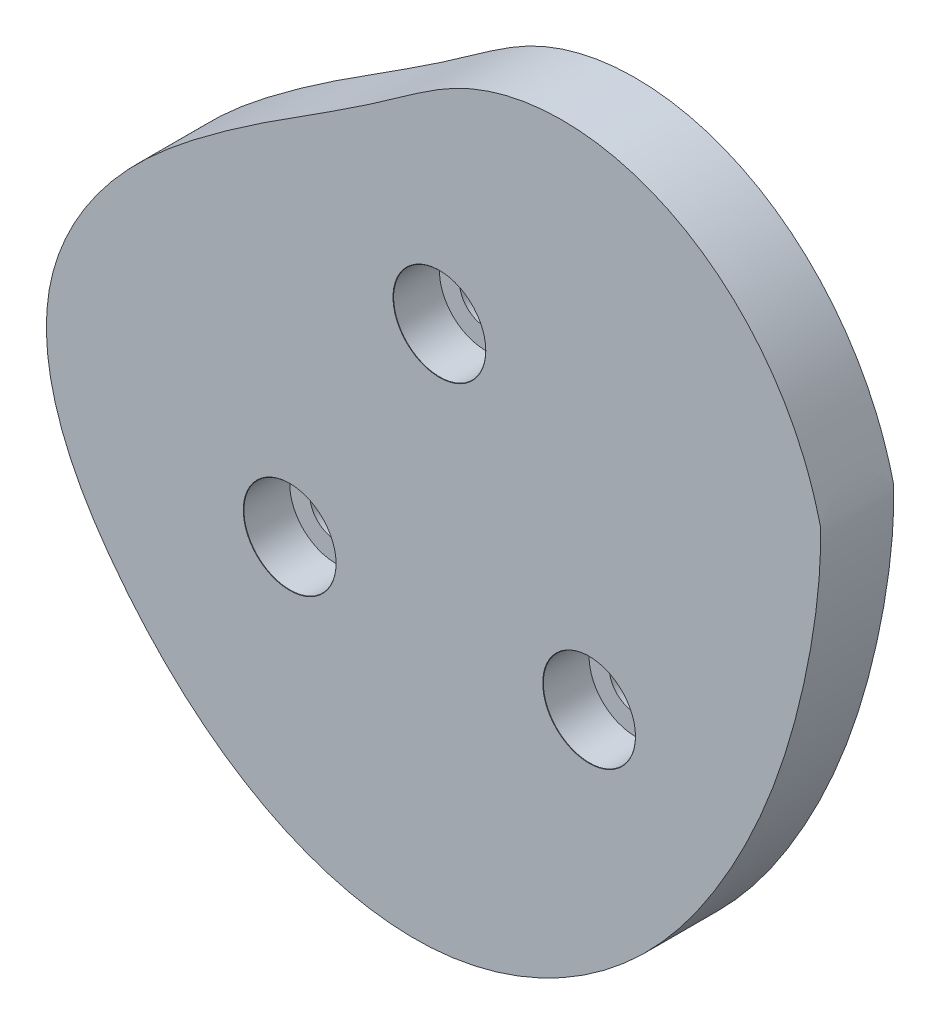
SolidWorks part; units mm, degrees
ref_plane "Front Plane" through (0, 0, 0) normal (0, 0, 1) x (1, 0, 0)
ref_plane "Top Plane" through (0, 0, 0) normal (0, 1, 0) x (1, 0, 0)
ref_plane "Right Plane" through (0, 0, 0) normal (1, 0, 0) x (0, 0, -1)
curve "Curve1"
  spline degree 3 poles (20.4719, -0.3582, 0) (20.4906, 0.0056, 0) (20.3791, 0.3547, 0) (20.2968, 0.7085, 0) (20.2014, 1.0583, 0) (20.1045, 1.4055, 0) (20.003, 1.7496, 0) (19.8979, 2.091, 0) (19.7889, 2.4294, 0) (19.6761, 2.7649, 0) (19.5596, 3.0976, 0) (19.4394, 3.4274, 0) (19.3156, 3.7542, 0) (19.1882, 4.0783, 0) (19.0573, 4.3994, 0) (18.9228, 4.7177, 0) (18.7848, 5.0331, 0) (18.6433, 5.3456, 0) (18.4984, 5.6553, 0) (18.3501, 5.962, 0) (18.1985, 6.266, 0) (18.0434, 6.567, 0) (17.8851, 6.8652, 0) (17.7235, 7.1605, 0) (17.5586, 7.4529, 0) (17.3904, 7.7425, 0) (17.219, 8.0291, 0) (17.0444, 8.3129, 0) (16.8666, 8.5937, 0) (16.6856, 8.8717, 0) (16.5014, 9.1467, 0) (16.3141, 9.4188, 0) (16.1237, 9.6879, 0) (15.9302, 9.9541, 0) (15.7336, 10.2173, 0) (15.5338, 10.4776, 0) (15.3311, 10.7348, 0) (15.1252, 10.989, 0) (14.9164, 11.2402, 0) (14.7045, 11.4883, 0) (14.4895, 11.7333, 0) (14.2716, 11.9752, 0) (14.0507, 12.214, 0) (13.8268, 12.4496, 0) (13.5999, 12.6821, 0) (13.3701, 12.9113, 0) (13.1374, 13.1373, 0) (12.9017, 13.3601, 0) (12.6631, 13.5795, 0) (12.4217, 13.7956, 0) (12.1773, 14.0084, 0) (11.9301, 14.2177, 0) (11.68, 14.4236, 0) (11.4271, 14.626, 0) (11.1713, 14.8249, 0) (10.9128, 15.0202, 0) (10.6515, 15.212, 0) (10.3875, 15.4001, 0) (10.1207, 15.5845, 0) (9.8512, 15.7652, 0) (9.579, 15.9422, 0) (9.3041, 16.1153, 0) (9.0266, 16.2845, 0) (8.7465, 16.4499, 0) (8.4638, 16.6112, 0) (8.1785, 16.7686, 0) (7.8907, 16.9219, 0) (7.6005, 17.0711, 0) (7.3077, 17.2161, 0) (7.0126, 17.357, 0) (6.715, 17.4935, 0) (6.4152, 17.6257, 0) (6.113, 17.7536, 0) (5.8085, 17.877, 0) (5.5018, 17.996, 0) (5.193, 18.1104, 0) (4.882, 18.2202, 0) (4.5689, 18.3254, 0) (4.2539, 18.4259, 0) (3.9368, 18.5217, 0) (3.6178, 18.6126, 0) (3.297, 18.6987, 0) (2.9743, 18.7798, 0) (2.6499, 18.856, 0) (2.3239, 18.9272, 0) (1.9962, 18.9933, 0) (1.6669, 19.0543, 0) (1.3362, 19.11, 0) (1.0041, 19.1606, 0) (0.6706, 19.2059, 0) (0.3358, 19.2458, 0) (-0.0001, 19.2804, 0) (-0.3372, 19.3095, 0) (-0.6752, 19.3332, 0) (-1.0143, 19.3513, 0) (-1.3542, 19.3639, 0) (-1.6948, 19.3709, 0) (-2.0362, 19.3722, 0) (-2.3782, 19.3678, 0) (-2.7207, 19.3577, 0) (-3.0636, 19.3418, 0) (-3.4068, 19.3201, 0) (-3.7502, 19.2926, 0) (-4.0938, 19.2592, 0) (-4.4374, 19.2198, 0) (-4.7809, 19.1746, 0) (-5.1242, 19.1233, 0) (-5.4672, 19.0661, 0) (-5.8099, 19.0029, 0) (-6.152, 18.9336, 0) (-6.4935, 18.8583, 0) (-6.8343, 18.7768, 0) (-7.1743, 18.6893, 0) (-7.5133, 18.5957, 0) (-7.8512, 18.496, 0) (-8.1879, 18.3901, 0) (-8.5233, 18.2781, 0) (-8.8573, 18.16, 0) (-9.1898, 18.0358, 0) (-9.5206, 17.9054, 0) (-9.8496, 17.7689, 0) (-10.1766, 17.6262, 0) (-10.5017, 17.4775, 0) (-10.8245, 17.3227, 0) (-11.1451, 17.1617, 0) (-11.4632, 16.9947, 0) (-11.7791, 16.822, 0) (-12.0927, 16.6439, 0) (-12.4044, 16.4609, 0) (-12.7144, 16.2733, 0) (-13.0229, 16.0815, 0) (-13.3301, 15.8857, 0) (-13.6364, 15.6864, 0) (-13.9422, 15.4837, 0) (-14.2476, 15.278, 0) (-14.5531, 15.0694, 0) (-14.859, 14.8581, 0) (-15.1658, 14.6444, 0) (-15.4738, 14.4285, 0) (-15.7835, 14.2103, 0) (-16.0953, 13.99, 0) (-16.4096, 13.7678, 0) (-16.7269, 13.5435, 0) (-17.0477, 13.3173, 0) (-17.3725, 13.0891, 0) (-17.7016, 12.8589, 0) (-18.0357, 12.6265, 0) (-18.3753, 12.3918, 0) (-18.7207, 12.1548, 0) (-19.0726, 11.9151, 0) (-19.4314, 11.6726, 0) (-19.7976, 11.4271, 0) (-20.1718, 11.1782, 0) (-20.5544, 10.9256, 0) (-20.9459, 10.669, 0) (-21.3468, 10.4079, 0) (-21.7576, 10.142, 0) (-22.1787, 9.8708, 0) (-22.6107, 9.5937, 0) (-23.0538, 9.3103, 0) (-23.5087, 9.0201, 0) (-23.9757, 8.7223, 0) (-24.4552, 8.4163, 0) (-24.9476, 8.1016, 0) (-25.4532, 7.7775, 0) (-25.9724, 7.443, 0) (-26.5055, 7.0977, 0) (-27.0528, 6.7405, 0) (-27.6146, 6.3708, 0) (-28.1911, 5.9877, 0) (-28.7826, 5.5902, 0) (-29.3891, 5.1775, 0) (-30.011, 4.7487, 0) (-30.6482, 4.3027, 0) (-31.3009, 3.8387, 0) (-31.9692, 3.3555, 0) (-32.6531, 2.8522, 0) (-33.3524, 2.3277, 0) (-34.0663, 1.7816, 0) (-34.7922, 1.212, 0) (-35.5264, 0.6179, 0) (-36.2656, -0.0015, 0) (-37.006, -0.6467, 0) (-37.7441, -1.3181, 0) (-38.4762, -2.0158, 0) (-39.1988, -2.7397, 0) (-39.9081, -3.4895, 0) (-40.6005, -4.2646, 0) (-41.2726, -5.0643, 0) (-41.9207, -5.8876, 0) (-42.5414, -6.7333, 0) (-43.1312, -7.6, 0) (-43.6867, -8.4861, 0) (-44.2047, -9.3896, 0) (-44.6819, -10.3087, 0) (-45.1152, -11.2411, 0) (-45.5015, -12.1842, 0) (-45.838, -13.1356, 0) (-46.1218, -14.0922, 0) (-46.3502, -15.0514, 0) (-46.5207, -16.0105, 0) (-46.6353, -16.9668, 0) (-46.6959, -17.9187, 0) (-46.7048, -18.8646, 0) (-46.6641, -19.8031, 0) (-46.576, -20.7331, 0) (-46.4429, -21.6534, 0) (-46.2667, -22.5631, 0) (-46.0499, -23.4614, 0) (-45.7945, -24.3476, 0) (-45.5028, -25.2212, 0) (-45.1769, -26.0818, 0) (-44.8189, -26.9291, 0) (-44.431, -27.763, 0) (-44.0152, -28.5834, 0) (-43.5736, -29.3905, 0) (-43.1082, -30.1845, 0) (-42.6208, -30.9657, 0) (-42.1134, -31.7347, 0) (-41.5877, -32.4919, 0) (-41.0455, -33.2381, 0) (-40.4886, -33.9741, 0) (-39.9184, -34.7007, 0) (-39.3348, -35.4173, 0) (-38.7375, -36.1234, 0) (-38.1264, -36.8183, 0) (-37.5012, -37.5012, 0) (-36.8618, -38.1715, 0) (-36.2081, -38.8285, 0) (-35.5401, -39.4713, 0) (-34.8578, -40.0993, 0) (-34.1611, -40.7116, 0) (-33.4502, -41.3075, 0) (-32.725, -41.8861, 0) (-31.9858, -42.4467, 0) (-31.2328, -42.9883, 0) (-30.4661, -43.5102, 0) (-29.686, -44.0114, 0) (-28.8928, -44.4912, 0) (-28.0869, -44.9487, 0) (-27.2687, -45.383, 0) (-26.4385, -45.7933, 0) (-25.5969, -46.1786, 0) (-24.7444, -46.5382, 0) (-23.8816, -46.8712, 0) (-23.009, -47.1767, 0) (-22.1274, -47.454, 0) (-21.2375, -47.7021, 0) (-20.34, -47.9203, 0) (-19.4357, -48.1077, 0) (-18.5254, -48.2636, 0) (-17.6101, -48.3873, 0) (-16.6907, -48.4779, 0) (-15.7681, -48.5348, 0) (-14.8434, -48.5572, 0) (-13.9176, -48.5444, 0) (-12.9919, -48.4959, 0) (-12.0676, -48.4109, 0) (-11.1461, -48.29, 0) (-10.2287, -48.1341, 0) (-9.3169, -47.9441, 0) (-8.412, -47.7209, 0) (-7.5154, -47.4656, 0) (-6.6283, -47.1791, 0) (-5.7518, -46.8626, 0) (-4.887, -46.5172, 0) (-4.035, -46.144, 0) (-3.1968, -45.7443, 0) (-2.3733, -45.3192, 0) (-1.5652, -44.87, 0) (-0.7734, -44.398, 0) (0.0014, -43.9045, 0) (0.7587, -43.3908, 0) (1.4978, -42.8582, 0) (2.2183, -42.3081, 0) (2.9197, -41.7419, 0) (3.6018, -41.1608, 0) (4.2642, -40.5664, 0) (4.9068, -39.9599, 0) (5.5294, -39.3427, 0) (6.132, -38.7162, 0) (6.7146, -38.0817, 0) (7.2773, -37.4407, 0) (7.8203, -36.7944, 0) (8.3437, -36.1442, 0) (8.8479, -35.4914, 0) (9.3333, -34.8372, 0) (9.8003, -34.183, 0) (10.2494, -33.5299, 0) (10.6811, -32.8793, 0) (11.0962, -32.2321, 0) (11.4952, -31.5897, 0) (11.8791, -30.953, 0) (12.2485, -30.3226, 0) (12.6037, -29.6986, 0) (12.9452, -29.0811, 0) (13.2733, -28.4704, 0) (13.5887, -27.8663, 0) (13.8917, -27.2691, 0) (14.1827, -26.6788, 0) (14.4623, -26.0953, 0) (14.7307, -25.5188, 0) (14.9884, -24.9492, 0) (15.2358, -24.3866, 0) (15.4733, -23.8309, 0) (15.7014, -23.2821, 0) (15.9202, -22.7402, 0) (16.1303, -22.2051, 0) (16.332, -21.6768, 0) (16.5257, -21.1552, 0) (16.7115, -20.6403, 0) (16.89, -20.1319, 0) (17.0614, -19.63, 0) (17.2261, -19.1344, 0) (17.3842, -18.6451, 0) (17.5361, -18.1619, 0) (17.6822, -17.6848, 0) (17.8225, -17.2135, 0) (17.9574, -16.748, 0) (18.0872, -16.2881, 0) (18.2121, -15.8337, 0) (18.3322, -15.3847, 0) (18.4478, -14.9408, 0) (18.5591, -14.5019, 0) (18.6662, -14.0679, 0) (18.7694, -13.6386, 0) (18.8688, -13.2138, 0) (18.9646, -12.7934, 0) (19.0568, -12.3772, 0) (19.1457, -11.9651, 0) (19.2313, -11.5568, 0) (19.3138, -11.1522, 0) (19.3933, -10.7511, 0) (19.4697, -10.3534, 0) (19.5433, -9.959, 0) (19.6141, -9.5675, 0) (19.6821, -9.1789, 0) (19.7474, -8.7931, 0) (19.8101, -8.4098, 0) (19.87, -8.0288, 0) (19.9274, -7.6502, 0) (19.9821, -7.2736, 0) (20.0342, -6.899, 0) (20.0836, -6.5262, 0) (20.1304, -6.1551, 0) (20.1746, -5.7855, 0) (20.216, -5.4173, 0) (20.2547, -5.0505, 0) (20.2905, -4.6848, 0) (20.3236, -4.3203, 0) (20.3537, -3.9567, 0) (20.3809, -3.594, 0) (20.4049, -3.2321, 0) (20.4259, -2.8709, 0) (20.4437, -2.5104, 0) (20.4581, -2.1504, 0) (20.4692, -1.791, 0) (20.4769, -1.432, 0) (20.4803, -1.0735, 0) (20.4824, -0.7151, 0) (20.4719, -0.3582, 0) (20.4906, 0.0056, 0) (20.3791, 0.3547, 0) knots -0.005175 -0.003449 -0.001724 0 0.001764 0.003519 0.005266 0.007004 0.008734 0.010456 0.01217 0.013877 0.015576 0.017268 0.018953 0.020632 0.022304 0.02397 0.02563 0.027283 0.028932 0.030575 0.032212 0.033845 0.035472 0.037095 0.038714 0.040328 0.041938 0.043545 0.045147 0.046746 0.048342 0.049935 0.051524 0.053111 0.054695 0.056276 0.057855 0.059432 0.061007 0.06258 0.064152 0.065721 0.06729 0.068857 0.070423 0.071988 0.073552 0.075115 0.076678 0.07824 0.079802 0.081364 0.082926 0.084488 0.08605 0.087612 0.089174 0.090737 0.092301 0.093865 0.095431 0.096997 0.098564 0.100132 0.101701 0.103272 0.104844 0.106418 0.107993 0.109569 0.111148 0.112728 0.11431 0.115894 0.117479 0.119067 0.120657 0.12225 0.123844 0.125441 0.12704 0.128642 0.130246 0.131852 0.133461 0.135073 0.136687 0.138304 0.139924 0.141547 0.143172 0.1448 0.146431 0.148065 0.149702 0.151342 0.152985 0.154631 0.156279 0.157931 0.159586 0.161244 0.162905 0.16457 0.166237 0.167907 0.169581 0.171258 0.172937 0.17462 0.176307 0.177996 0.179688 0.181384 0.183082 0.184784 0.186489 0.188197 0.189908 0.191622 0.19334 0.19506 0.196783 0.19851 0.200239 0.201971 0.203707 0.205446 0.207188 0.208935 0.210686 0.212442 0.214204 0.215972 0.217748 0.219531 0.221323 0.223125 0.224939 0.226765 0.228604 0.23046 0.232333 0.234225 0.236138 0.238074 0.240035 0.242024 0.244043 0.246095 0.248182 0.250307 0.252473 0.254682 0.256938 0.259244 0.261602 0.264016 0.26649 0.269025 0.271625 0.274295 0.277036 0.279852 0.282747 0.285724 0.288785 0.291935 0.295176 0.298513 0.301947 0.305484 0.309124 0.312873 0.316734 0.320709 0.324801 0.329015 0.333352 0.337803 0.34236 0.347013 0.351751 0.356565 0.361444 0.366378 0.371357 0.376371 0.38141 0.386464 0.391524 0.39658 0.401624 0.406647 0.411641 0.416599 0.421513 0.426378 0.431188 0.43594 0.440632 0.445271 0.449865 0.454421 0.458946 0.463447 0.467927 0.472391 0.476844 0.481289 0.485727 0.490163 0.494596 0.499029 0.503463 0.507898 0.512334 0.516773 0.521215 0.525659 0.530106 0.534555 0.539008 0.543464 0.547923 0.552384 0.556848 0.561315 0.565783 0.570252 0.574723 0.579195 0.583667 0.588139 0.592612 0.597084 0.601555 0.606025 0.610494 0.614962 0.619428 0.623892 0.628354 0.632814 0.637273 0.641729 0.646184 0.650638 0.65509 0.659542 0.663994 0.668446 0.672899 0.677354 0.681812 0.686275 0.690742 0.695217 0.699697 0.704183 0.708673 0.713166 0.717661 0.722155 0.726648 0.731137 0.735622 0.740099 0.744568 0.749025 0.75347 0.757899 0.762311 0.766703 0.771074 0.775421 0.779741 0.784033 0.788293 0.792521 0.796712 0.800866 0.804979 0.809049 0.813074 0.817052 0.82098 0.824856 0.828677 0.832443 0.83615 0.839797 0.843382 0.846904 0.850365 0.853767 0.857109 0.860394 0.863623 0.866796 0.869914 0.87298 0.875994 0.878957 0.88187 0.884735 0.887552 0.890324 0.89305 0.895732 0.898371 0.900968 0.903525 0.906043 0.908522 0.910963 0.913369 0.915739 0.918076 0.920379 0.922651 0.924892 0.927103 0.929285 0.93144 0.933569 0.935672 0.93775 0.939805 0.941838 0.943849 0.94584 0.94781 0.949763 0.951697 0.953615 0.955517 0.957403 0.959276 0.961134 0.962981 0.964815 0.966638 0.968451 0.970255 0.972049 0.973835 0.975613 0.977385 0.979149 0.980908 0.982662 0.98441 0.986154 0.987894 0.989631 0.991365 0.993096 0.994825 0.996551 0.998276 1 1.001764 1.003519 1.005266 periodic
sketch "Sketch1" plane through (0, 0, 0) normal (0, 0, 1) x (1, 0, 0)
  spline S0 degree 3 poles (20.4719, -0.3582) (20.4906, 0.0056) (20.3791, 0.3547) (20.2968, 0.7085) (20.2014, 1.0583) (20.1045, 1.4055) (20.003, 1.7496) (19.8979, 2.091) (19.7889, 2.4294) (19.6761, 2.7649) (19.5596, 3.0976) (19.4394, 3.4274) (19.3156, 3.7542) (19.1882, 4.0783) (19.0573, 4.3994) (18.9228, 4.7177) (18.7848, 5.0331) (18.6433, 5.3456) (18.4984, 5.6553) (18.3501, 5.962) (18.1985, 6.266) (18.0434, 6.567) (17.8851, 6.8652) (17.7235, 7.1605) (17.5586, 7.4529) (17.3904, 7.7425) (17.219, 8.0291) (17.0444, 8.3129) (16.8666, 8.5937) (16.6856, 8.8717) (16.5014, 9.1467) (16.3141, 9.4188) (16.1237, 9.6879) (15.9302, 9.9541) (15.7336, 10.2173) (15.5338, 10.4776) (15.3311, 10.7348) (15.1252, 10.989) (14.9164, 11.2402) (14.7045, 11.4883) (14.4895, 11.7333) (14.2716, 11.9752) (14.0507, 12.214) (13.8268, 12.4496) (13.5999, 12.6821) (13.3701, 12.9113) (13.1374, 13.1373) (12.9017, 13.3601) (12.6631, 13.5795) (12.4217, 13.7956) (12.1773, 14.0084) (11.9301, 14.2177) (11.68, 14.4236) (11.4271, 14.626) (11.1713, 14.8249) (10.9128, 15.0202) (10.6515, 15.212) (10.3875, 15.4001) (10.1207, 15.5845) (9.8512, 15.7652) (9.579, 15.9422) (9.3041, 16.1153) (9.0266, 16.2845) (8.7465, 16.4499) (8.4638, 16.6112) (8.1785, 16.7686) (7.8907, 16.9219) (7.6005, 17.0711) (7.3077, 17.2161) (7.0126, 17.357) (6.715, 17.4935) (6.4152, 17.6257) (6.113, 17.7536) (5.8085, 17.877) (5.5018, 17.996) (5.193, 18.1104) (4.882, 18.2202) (4.5689, 18.3254) (4.2539, 18.4259) (3.9368, 18.5217) (3.6178, 18.6126) (3.297, 18.6987) (2.9743, 18.7798) (2.6499, 18.856) (2.3239, 18.9272) (1.9962, 18.9933) (1.6669, 19.0543) (1.3362, 19.11) (1.0041, 19.1606) (0.6706, 19.2059) (0.3358, 19.2458) (-0.0001, 19.2804) (-0.3372, 19.3095) (-0.6752, 19.3332) (-1.0143, 19.3513) (-1.3542, 19.3639) (-1.6948, 19.3709) (-2.0362, 19.3722) (-2.3782, 19.3678) (-2.7207, 19.3577) (-3.0636, 19.3418) (-3.4068, 19.3201) (-3.7502, 19.2926) (-4.0938, 19.2592) (-4.4374, 19.2198) (-4.7809, 19.1746) (-5.1242, 19.1233) (-5.4672, 19.0661) (-5.8099, 19.0029) (-6.152, 18.9336) (-6.4935, 18.8583) (-6.8343, 18.7768) (-7.1743, 18.6893) (-7.5133, 18.5957) (-7.8512, 18.496) (-8.1879, 18.3901) (-8.5233, 18.2781) (-8.8573, 18.16) (-9.1898, 18.0358) (-9.5206, 17.9054) (-9.8496, 17.7689) (-10.1766, 17.6262) (-10.5017, 17.4775) (-10.8245, 17.3227) (-11.1451, 17.1617) (-11.4632, 16.9947) (-11.7791, 16.822) (-12.0927, 16.6439) (-12.4044, 16.4609) (-12.7144, 16.2733) (-13.0229, 16.0815) (-13.3301, 15.8857) (-13.6364, 15.6864) (-13.9422, 15.4837) (-14.2476, 15.278) (-14.5531, 15.0694) (-14.859, 14.8581) (-15.1658, 14.6444) (-15.4738, 14.4285) (-15.7835, 14.2103) (-16.0953, 13.99) (-16.4096, 13.7678) (-16.7269, 13.5435) (-17.0477, 13.3173) (-17.3725, 13.0891) (-17.7016, 12.8589) (-18.0357, 12.6265) (-18.3753, 12.3918) (-18.7207, 12.1548) (-19.0726, 11.9151) (-19.4314, 11.6726) (-19.7976, 11.4271) (-20.1718, 11.1782) (-20.5544, 10.9256) (-20.9459, 10.669) (-21.3468, 10.4079) (-21.7576, 10.142) (-22.1787, 9.8708) (-22.6107, 9.5937) (-23.0538, 9.3103) (-23.5087, 9.0201) (-23.9757, 8.7223) (-24.4552, 8.4163) (-24.9476, 8.1016) (-25.4532, 7.7775) (-25.9724, 7.443) (-26.5055, 7.0977) (-27.0528, 6.7405) (-27.6146, 6.3708) (-28.1911, 5.9877) (-28.7826, 5.5902) (-29.3891, 5.1775) (-30.011, 4.7487) (-30.6482, 4.3027) (-31.3009, 3.8387) (-31.9692, 3.3555) (-32.6531, 2.8522) (-33.3524, 2.3277) (-34.0663, 1.7816) (-34.7922, 1.212) (-35.5264, 0.6179) (-36.2656, -0.0015) (-37.006, -0.6467) (-37.7441, -1.3181) (-38.4762, -2.0158) (-39.1988, -2.7397) (-39.9081, -3.4895) (-40.6005, -4.2646) (-41.2726, -5.0643) (-41.9207, -5.8876) (-42.5414, -6.7333) (-43.1312, -7.6) (-43.6867, -8.4861) (-44.2047, -9.3896) (-44.6819, -10.3087) (-45.1152, -11.2411) (-45.5015, -12.1842) (-45.838, -13.1356) (-46.1218, -14.0922) (-46.3502, -15.0514) (-46.5207, -16.0105) (-46.6353, -16.9668) (-46.6959, -17.9187) (-46.7048, -18.8646) (-46.6641, -19.8031) (-46.576, -20.7331) (-46.4429, -21.6534) (-46.2667, -22.5631) (-46.0499, -23.4614) (-45.7945, -24.3476) (-45.5028, -25.2212) (-45.1769, -26.0818) (-44.8189, -26.9291) (-44.431, -27.763) (-44.0152, -28.5834) (-43.5736, -29.3905) (-43.1082, -30.1845) (-42.6208, -30.9657) (-42.1134, -31.7347) (-41.5877, -32.4919) (-41.0455, -33.2381) (-40.4886, -33.9741) (-39.9184, -34.7007) (-39.3348, -35.4173) (-38.7375, -36.1234) (-38.1264, -36.8183) (-37.5012, -37.5012) (-36.8618, -38.1715) (-36.2081, -38.8285) (-35.5401, -39.4713) (-34.8578, -40.0993) (-34.1611, -40.7116) (-33.4502, -41.3075) (-32.725, -41.8861) (-31.9858, -42.4467) (-31.2328, -42.9883) (-30.4661, -43.5102) (-29.686, -44.0114) (-28.8928, -44.4912) (-28.0869, -44.9487) (-27.2687, -45.383) (-26.4385, -45.7933) (-25.5969, -46.1786) (-24.7444, -46.5382) (-23.8816, -46.8712) (-23.009, -47.1767) (-22.1274, -47.454) (-21.2375, -47.7021) (-20.34, -47.9203) (-19.4357, -48.1077) (-18.5254, -48.2636) (-17.6101, -48.3873) (-16.6907, -48.4779) (-15.7681, -48.5348) (-14.8434, -48.5572) (-13.9176, -48.5444) (-12.9919, -48.4959) (-12.0676, -48.4109) (-11.1461, -48.29) (-10.2287, -48.1341) (-9.3169, -47.9441) (-8.412, -47.7209) (-7.5154, -47.4656) (-6.6283, -47.1791) (-5.7518, -46.8626) (-4.887, -46.5172) (-4.035, -46.144) (-3.1968, -45.7443) (-2.3733, -45.3192) (-1.5652, -44.87) (-0.7734, -44.398) (0.0014, -43.9045) (0.7587, -43.3908) (1.4978, -42.8582) (2.2183, -42.3081) (2.9197, -41.7419) (3.6018, -41.1608) (4.2642, -40.5664) (4.9068, -39.9599) (5.5294, -39.3427) (6.132, -38.7162) (6.7146, -38.0817) (7.2773, -37.4407) (7.8203, -36.7944) (8.3437, -36.1442) (8.8479, -35.4914) (9.3333, -34.8372) (9.8003, -34.183) (10.2494, -33.5299) (10.6811, -32.8793) (11.0962, -32.2321) (11.4952, -31.5897) (11.8791, -30.953) (12.2485, -30.3226) (12.6037, -29.6986) (12.9452, -29.0811) (13.2733, -28.4704) (13.5887, -27.8663) (13.8917, -27.2691) (14.1827, -26.6788) (14.4623, -26.0953) (14.7307, -25.5188) (14.9884, -24.9492) (15.2358, -24.3866) (15.4733, -23.8309) (15.7014, -23.2821) (15.9202, -22.7402) (16.1303, -22.2051) (16.332, -21.6768) (16.5257, -21.1552) (16.7115, -20.6403) (16.89, -20.1319) (17.0614, -19.63) (17.2261, -19.1344) (17.3842, -18.6451) (17.5361, -18.1619) (17.6822, -17.6848) (17.8225, -17.2135) (17.9574, -16.748) (18.0872, -16.2881) (18.2121, -15.8337) (18.3322, -15.3847) (18.4478, -14.9408) (18.5591, -14.5019) (18.6662, -14.0679) (18.7694, -13.6386) (18.8688, -13.2138) (18.9646, -12.7934) (19.0568, -12.3772) (19.1457, -11.9651) (19.2313, -11.5568) (19.3138, -11.1522) (19.3933, -10.7511) (19.4697, -10.3534) (19.5433, -9.959) (19.6141, -9.5675) (19.6821, -9.1789) (19.7474, -8.7931) (19.8101, -8.4098) (19.87, -8.0288) (19.9274, -7.6502) (19.9821, -7.2736) (20.0342, -6.899) (20.0836, -6.5262) (20.1304, -6.1551) (20.1746, -5.7855) (20.216, -5.4173) (20.2547, -5.0505) (20.2905, -4.6848) (20.3236, -4.3203) (20.3537, -3.9567) (20.3809, -3.594) (20.4049, -3.2321) (20.4259, -2.8709) (20.4437, -2.5104) (20.4581, -2.1504) (20.4692, -1.791) (20.4769, -1.432) (20.4803, -1.0735) (20.4824, -0.7151) (20.4719, -0.3582) (20.4906, 0.0056) (20.3791, 0.3547) knots -0.005175 -0.003449 -0.001724 0 0.001764 0.003519 0.005266 0.007004 0.008734 0.010456 0.01217 0.013877 0.015576 0.017268 0.018953 0.020632 0.022304 0.02397 0.02563 0.027283 0.028932 0.030575 0.032212 0.033845 0.035472 0.037095 0.038714 0.040328 0.041938 0.043545 0.045147 0.046746 0.048342 0.049935 0.051524 0.053111 0.054695 0.056276 0.057855 0.059432 0.061007 0.06258 0.064152 0.065721 0.06729 0.068857 0.070423 0.071988 0.073552 0.075115 0.076678 0.07824 0.079802 0.081364 0.082926 0.084488 0.08605 0.087612 0.089174 0.090737 0.092301 0.093865 0.095431 0.096997 0.098564 0.100132 0.101701 0.103272 0.104844 0.106418 0.107993 0.109569 0.111148 0.112728 0.11431 0.115894 0.117479 0.119067 0.120657 0.12225 0.123844 0.125441 0.12704 0.128642 0.130246 0.131852 0.133461 0.135073 0.136687 0.138304 0.139924 0.141547 0.143172 0.1448 0.146431 0.148065 0.149702 0.151342 0.152985 0.154631 0.156279 0.157931 0.159586 0.161244 0.162905 0.16457 0.166237 0.167907 0.169581 0.171258 0.172937 0.17462 0.176307 0.177996 0.179688 0.181384 0.183082 0.184784 0.186489 0.188197 0.189908 0.191622 0.19334 0.19506 0.196783 0.19851 0.200239 0.201971 0.203707 0.205446 0.207188 0.208935 0.210686 0.212442 0.214204 0.215972 0.217748 0.219531 0.221323 0.223125 0.224939 0.226765 0.228604 0.23046 0.232333 0.234225 0.236138 0.238074 0.240035 0.242024 0.244043 0.246095 0.248182 0.250307 0.252473 0.254682 0.256938 0.259244 0.261602 0.264016 0.26649 0.269025 0.271625 0.274295 0.277036 0.279852 0.282747 0.285724 0.288785 0.291935 0.295176 0.298513 0.301947 0.305484 0.309124 0.312873 0.316734 0.320709 0.324801 0.329015 0.333352 0.337803 0.34236 0.347013 0.351751 0.356565 0.361444 0.366378 0.371357 0.376371 0.38141 0.386464 0.391524 0.39658 0.401624 0.406647 0.411641 0.416599 0.421513 0.426378 0.431188 0.43594 0.440632 0.445271 0.449865 0.454421 0.458946 0.463447 0.467927 0.472391 0.476844 0.481289 0.485727 0.490163 0.494596 0.499029 0.503463 0.507898 0.512334 0.516773 0.521215 0.525659 0.530106 0.534555 0.539008 0.543464 0.547923 0.552384 0.556848 0.561315 0.565783 0.570252 0.574723 0.579195 0.583667 0.588139 0.592612 0.597084 0.601555 0.606025 0.610494 0.614962 0.619428 0.623892 0.628354 0.632814 0.637273 0.641729 0.646184 0.650638 0.65509 0.659542 0.663994 0.668446 0.672899 0.677354 0.681812 0.686275 0.690742 0.695217 0.699697 0.704183 0.708673 0.713166 0.717661 0.722155 0.726648 0.731137 0.735622 0.740099 0.744568 0.749025 0.75347 0.757899 0.762311 0.766703 0.771074 0.775421 0.779741 0.784033 0.788293 0.792521 0.796712 0.800866 0.804979 0.809049 0.813074 0.817052 0.82098 0.824856 0.828677 0.832443 0.83615 0.839797 0.843382 0.846904 0.850365 0.853767 0.857109 0.860394 0.863623 0.866796 0.869914 0.87298 0.875994 0.878957 0.88187 0.884735 0.887552 0.890324 0.89305 0.895732 0.898371 0.900968 0.903525 0.906043 0.908522 0.910963 0.913369 0.915739 0.918076 0.920379 0.922651 0.924892 0.927103 0.929285 0.93144 0.933569 0.935672 0.93775 0.939805 0.941838 0.943849 0.94584 0.94781 0.949763 0.951697 0.953615 0.955517 0.957403 0.959276 0.961134 0.962981 0.964815 0.966638 0.968451 0.970255 0.972049 0.973835 0.975613 0.977385 0.979149 0.980908 0.982662 0.98441 0.986154 0.987894 0.989631 0.991365 0.993096 0.994825 0.996551 0.998276 1 1.001764 1.003519 1.005266 only from (20.4693, 0) to (20.4693, 0) construction
  spline S1 degree 3 poles (20.4719, -0.3582) (20.4906, 0.0056) (20.3791, 0.3547) (20.2968, 0.7085) (20.2014, 1.0583) (20.1045, 1.4055) (20.003, 1.7496) (19.8979, 2.091) (19.7889, 2.4294) (19.6761, 2.7649) (19.5596, 3.0976) (19.4394, 3.4274) (19.3156, 3.7542) (19.1882, 4.0783) (19.0573, 4.3994) (18.9228, 4.7177) (18.7848, 5.0331) (18.6433, 5.3456) (18.4984, 5.6553) (18.3501, 5.962) (18.1985, 6.266) (18.0434, 6.567) (17.8851, 6.8652) (17.7235, 7.1605) (17.5586, 7.4529) (17.3904, 7.7425) (17.219, 8.0291) (17.0444, 8.3129) (16.8666, 8.5937) (16.6856, 8.8717) (16.5014, 9.1467) (16.3141, 9.4188) (16.1237, 9.6879) (15.9302, 9.9541) (15.7336, 10.2173) (15.5338, 10.4776) (15.3311, 10.7348) (15.1252, 10.989) (14.9164, 11.2402) (14.7045, 11.4883) (14.4895, 11.7333) (14.2716, 11.9752) (14.0507, 12.214) (13.8268, 12.4496) (13.5999, 12.6821) (13.3701, 12.9113) (13.1374, 13.1373) (12.9017, 13.3601) (12.6631, 13.5795) (12.4217, 13.7956) (12.1773, 14.0084) (11.9301, 14.2177) (11.68, 14.4236) (11.4271, 14.626) (11.1713, 14.8249) (10.9128, 15.0202) (10.6515, 15.212) (10.3875, 15.4001) (10.1207, 15.5845) (9.8512, 15.7652) (9.579, 15.9422) (9.3041, 16.1153) (9.0266, 16.2845) (8.7465, 16.4499) (8.4638, 16.6112) (8.1785, 16.7686) (7.8907, 16.9219) (7.6005, 17.0711) (7.3077, 17.2161) (7.0126, 17.357) (6.715, 17.4935) (6.4152, 17.6257) (6.113, 17.7536) (5.8085, 17.877) (5.5018, 17.996) (5.193, 18.1104) (4.882, 18.2202) (4.5689, 18.3254) (4.2539, 18.4259) (3.9368, 18.5217) (3.6178, 18.6126) (3.297, 18.6987) (2.9743, 18.7798) (2.6499, 18.856) (2.3239, 18.9272) (1.9962, 18.9933) (1.6669, 19.0543) (1.3362, 19.11) (1.0041, 19.1606) (0.6706, 19.2059) (0.3358, 19.2458) (-0.0001, 19.2804) (-0.3372, 19.3095) (-0.6752, 19.3332) (-1.0143, 19.3513) (-1.3542, 19.3639) (-1.6948, 19.3709) (-2.0362, 19.3722) (-2.3782, 19.3678) (-2.7207, 19.3577) (-3.0636, 19.3418) (-3.4068, 19.3201) (-3.7502, 19.2926) (-4.0938, 19.2592) (-4.4374, 19.2198) (-4.7809, 19.1746) (-5.1242, 19.1233) (-5.4672, 19.0661) (-5.8099, 19.0029) (-6.152, 18.9336) (-6.4935, 18.8583) (-6.8343, 18.7768) (-7.1743, 18.6893) (-7.5133, 18.5957) (-7.8512, 18.496) (-8.1879, 18.3901) (-8.5233, 18.2781) (-8.8573, 18.16) (-9.1898, 18.0358) (-9.5206, 17.9054) (-9.8496, 17.7689) (-10.1766, 17.6262) (-10.5017, 17.4775) (-10.8245, 17.3227) (-11.1451, 17.1617) (-11.4632, 16.9947) (-11.7791, 16.822) (-12.0927, 16.6439) (-12.4044, 16.4609) (-12.7144, 16.2733) (-13.0229, 16.0815) (-13.3301, 15.8857) (-13.6364, 15.6864) (-13.9422, 15.4837) (-14.2476, 15.278) (-14.5531, 15.0694) (-14.859, 14.8581) (-15.1658, 14.6444) (-15.4738, 14.4285) (-15.7835, 14.2103) (-16.0953, 13.99) (-16.4096, 13.7678) (-16.7269, 13.5435) (-17.0477, 13.3173) (-17.3725, 13.0891) (-17.7016, 12.8589) (-18.0357, 12.6265) (-18.3753, 12.3918) (-18.7207, 12.1548) (-19.0726, 11.9151) (-19.4314, 11.6726) (-19.7976, 11.4271) (-20.1718, 11.1782) (-20.5544, 10.9256) (-20.9459, 10.669) (-21.3468, 10.4079) (-21.7576, 10.142) (-22.1787, 9.8708) (-22.6107, 9.5937) (-23.0538, 9.3103) (-23.5087, 9.0201) (-23.9757, 8.7223) (-24.4552, 8.4163) (-24.9476, 8.1016) (-25.4532, 7.7775) (-25.9724, 7.443) (-26.5055, 7.0977) (-27.0528, 6.7405) (-27.6146, 6.3708) (-28.1911, 5.9877) (-28.7826, 5.5902) (-29.3891, 5.1775) (-30.011, 4.7487) (-30.6482, 4.3027) (-31.3009, 3.8387) (-31.9692, 3.3555) (-32.6531, 2.8522) (-33.3524, 2.3277) (-34.0663, 1.7816) (-34.7922, 1.212) (-35.5264, 0.6179) (-36.2656, -0.0015) (-37.006, -0.6467) (-37.7441, -1.3181) (-38.4762, -2.0158) (-39.1988, -2.7397) (-39.9081, -3.4895) (-40.6005, -4.2646) (-41.2726, -5.0643) (-41.9207, -5.8876) (-42.5414, -6.7333) (-43.1312, -7.6) (-43.6867, -8.4861) (-44.2047, -9.3896) (-44.6819, -10.3087) (-45.1152, -11.2411) (-45.5015, -12.1842) (-45.838, -13.1356) (-46.1218, -14.0922) (-46.3502, -15.0514) (-46.5207, -16.0105) (-46.6353, -16.9668) (-46.6959, -17.9187) (-46.7048, -18.8646) (-46.6641, -19.8031) (-46.576, -20.7331) (-46.4429, -21.6534) (-46.2667, -22.5631) (-46.0499, -23.4614) (-45.7945, -24.3476) (-45.5028, -25.2212) (-45.1769, -26.0818) (-44.8189, -26.9291) (-44.431, -27.763) (-44.0152, -28.5834) (-43.5736, -29.3905) (-43.1082, -30.1845) (-42.6208, -30.9657) (-42.1134, -31.7347) (-41.5877, -32.4919) (-41.0455, -33.2381) (-40.4886, -33.9741) (-39.9184, -34.7007) (-39.3348, -35.4173) (-38.7375, -36.1234) (-38.1264, -36.8183) (-37.5012, -37.5012) (-36.8618, -38.1715) (-36.2081, -38.8285) (-35.5401, -39.4713) (-34.8578, -40.0993) (-34.1611, -40.7116) (-33.4502, -41.3075) (-32.725, -41.8861) (-31.9858, -42.4467) (-31.2328, -42.9883) (-30.4661, -43.5102) (-29.686, -44.0114) (-28.8928, -44.4912) (-28.0869, -44.9487) (-27.2687, -45.383) (-26.4385, -45.7933) (-25.5969, -46.1786) (-24.7444, -46.5382) (-23.8816, -46.8712) (-23.009, -47.1767) (-22.1274, -47.454) (-21.2375, -47.7021) (-20.34, -47.9203) (-19.4357, -48.1077) (-18.5254, -48.2636) (-17.6101, -48.3873) (-16.6907, -48.4779) (-15.7681, -48.5348) (-14.8434, -48.5572) (-13.9176, -48.5444) (-12.9919, -48.4959) (-12.0676, -48.4109) (-11.1461, -48.29) (-10.2287, -48.1341) (-9.3169, -47.9441) (-8.412, -47.7209) (-7.5154, -47.4656) (-6.6283, -47.1791) (-5.7518, -46.8626) (-4.887, -46.5172) (-4.035, -46.144) (-3.1968, -45.7443) (-2.3733, -45.3192) (-1.5652, -44.87) (-0.7734, -44.398) (0.0014, -43.9045) (0.7587, -43.3908) (1.4978, -42.8582) (2.2183, -42.3081) (2.9197, -41.7419) (3.6018, -41.1608) (4.2642, -40.5664) (4.9068, -39.9599) (5.5294, -39.3427) (6.132, -38.7162) (6.7146, -38.0817) (7.2773, -37.4407) (7.8203, -36.7944) (8.3437, -36.1442) (8.8479, -35.4914) (9.3333, -34.8372) (9.8003, -34.183) (10.2494, -33.5299) (10.6811, -32.8793) (11.0962, -32.2321) (11.4952, -31.5897) (11.8791, -30.953) (12.2485, -30.3226) (12.6037, -29.6986) (12.9452, -29.0811) (13.2733, -28.4704) (13.5887, -27.8663) (13.8917, -27.2691) (14.1827, -26.6788) (14.4623, -26.0953) (14.7307, -25.5188) (14.9884, -24.9492) (15.2358, -24.3866) (15.4733, -23.8309) (15.7014, -23.2821) (15.9202, -22.7402) (16.1303, -22.2051) (16.332, -21.6768) (16.5257, -21.1552) (16.7115, -20.6403) (16.89, -20.1319) (17.0614, -19.63) (17.2261, -19.1344) (17.3842, -18.6451) (17.5361, -18.1619) (17.6822, -17.6848) (17.8225, -17.2135) (17.9574, -16.748) (18.0872, -16.2881) (18.2121, -15.8337) (18.3322, -15.3847) (18.4478, -14.9408) (18.5591, -14.5019) (18.6662, -14.0679) (18.7694, -13.6386) (18.8688, -13.2138) (18.9646, -12.7934) (19.0568, -12.3772) (19.1457, -11.9651) (19.2313, -11.5568) (19.3138, -11.1522) (19.3933, -10.7511) (19.4697, -10.3534) (19.5433, -9.959) (19.6141, -9.5675) (19.6821, -9.1789) (19.7474, -8.7931) (19.8101, -8.4098) (19.87, -8.0288) (19.9274, -7.6502) (19.9821, -7.2736) (20.0342, -6.899) (20.0836, -6.5262) (20.1304, -6.1551) (20.1746, -5.7855) (20.216, -5.4173) (20.2547, -5.0505) (20.2905, -4.6848) (20.3236, -4.3203) (20.3537, -3.9567) (20.3809, -3.594) (20.4049, -3.2321) (20.4259, -2.8709) (20.4437, -2.5104) (20.4581, -2.1504) (20.4692, -1.791) (20.4769, -1.432) (20.4803, -1.0735) (20.4824, -0.7151) (20.4719, -0.3582) (20.4906, 0.0056) (20.3791, 0.3547) knots -0.005175 -0.003449 -0.001724 0 0.001764 0.003519 0.005266 0.007004 0.008734 0.010456 0.01217 0.013877 0.015576 0.017268 0.018953 0.020632 0.022304 0.02397 0.02563 0.027283 0.028932 0.030575 0.032212 0.033845 0.035472 0.037095 0.038714 0.040328 0.041938 0.043545 0.045147 0.046746 0.048342 0.049935 0.051524 0.053111 0.054695 0.056276 0.057855 0.059432 0.061007 0.06258 0.064152 0.065721 0.06729 0.068857 0.070423 0.071988 0.073552 0.075115 0.076678 0.07824 0.079802 0.081364 0.082926 0.084488 0.08605 0.087612 0.089174 0.090737 0.092301 0.093865 0.095431 0.096997 0.098564 0.100132 0.101701 0.103272 0.104844 0.106418 0.107993 0.109569 0.111148 0.112728 0.11431 0.115894 0.117479 0.119067 0.120657 0.12225 0.123844 0.125441 0.12704 0.128642 0.130246 0.131852 0.133461 0.135073 0.136687 0.138304 0.139924 0.141547 0.143172 0.1448 0.146431 0.148065 0.149702 0.151342 0.152985 0.154631 0.156279 0.157931 0.159586 0.161244 0.162905 0.16457 0.166237 0.167907 0.169581 0.171258 0.172937 0.17462 0.176307 0.177996 0.179688 0.181384 0.183082 0.184784 0.186489 0.188197 0.189908 0.191622 0.19334 0.19506 0.196783 0.19851 0.200239 0.201971 0.203707 0.205446 0.207188 0.208935 0.210686 0.212442 0.214204 0.215972 0.217748 0.219531 0.221323 0.223125 0.224939 0.226765 0.228604 0.23046 0.232333 0.234225 0.236138 0.238074 0.240035 0.242024 0.244043 0.246095 0.248182 0.250307 0.252473 0.254682 0.256938 0.259244 0.261602 0.264016 0.26649 0.269025 0.271625 0.274295 0.277036 0.279852 0.282747 0.285724 0.288785 0.291935 0.295176 0.298513 0.301947 0.305484 0.309124 0.312873 0.316734 0.320709 0.324801 0.329015 0.333352 0.337803 0.34236 0.347013 0.351751 0.356565 0.361444 0.366378 0.371357 0.376371 0.38141 0.386464 0.391524 0.39658 0.401624 0.406647 0.411641 0.416599 0.421513 0.426378 0.431188 0.43594 0.440632 0.445271 0.449865 0.454421 0.458946 0.463447 0.467927 0.472391 0.476844 0.481289 0.485727 0.490163 0.494596 0.499029 0.503463 0.507898 0.512334 0.516773 0.521215 0.525659 0.530106 0.534555 0.539008 0.543464 0.547923 0.552384 0.556848 0.561315 0.565783 0.570252 0.574723 0.579195 0.583667 0.588139 0.592612 0.597084 0.601555 0.606025 0.610494 0.614962 0.619428 0.623892 0.628354 0.632814 0.637273 0.641729 0.646184 0.650638 0.65509 0.659542 0.663994 0.668446 0.672899 0.677354 0.681812 0.686275 0.690742 0.695217 0.699697 0.704183 0.708673 0.713166 0.717661 0.722155 0.726648 0.731137 0.735622 0.740099 0.744568 0.749025 0.75347 0.757899 0.762311 0.766703 0.771074 0.775421 0.779741 0.784033 0.788293 0.792521 0.796712 0.800866 0.804979 0.809049 0.813074 0.817052 0.82098 0.824856 0.828677 0.832443 0.83615 0.839797 0.843382 0.846904 0.850365 0.853767 0.857109 0.860394 0.863623 0.866796 0.869914 0.87298 0.875994 0.878957 0.88187 0.884735 0.887552 0.890324 0.89305 0.895732 0.898371 0.900968 0.903525 0.906043 0.908522 0.910963 0.913369 0.915739 0.918076 0.920379 0.922651 0.924892 0.927103 0.929285 0.93144 0.933569 0.935672 0.93775 0.939805 0.941838 0.943849 0.94584 0.94781 0.949763 0.951697 0.953615 0.955517 0.957403 0.959276 0.961134 0.962981 0.964815 0.966638 0.968451 0.970255 0.972049 0.973835 0.975613 0.977385 0.979149 0.980908 0.982662 0.98441 0.986154 0.987894 0.989631 0.991365 0.993096 0.994825 0.996551 0.998276 1 1.001764 1.003519 1.005266 only from (20.4693, 0) to (20.4693, 0)
extrude "Boss-Extrude1" add sketch "Sketch1" along normal mid plane 6.35
sketch "Sketch4" plane through (0, 0, 3.175) normal (0, 0, 1) x (1, 0, 0)
  line L0 (17.7659, -20.9602) -> (-1.4085, -53.5016) construction
  line L1 (-50.4616, -14.4148) -> (-15.5658, 21.7389) construction
  circle A0 centre (-12.5939, -16.2726) radius 28.5365 construction
  spline S0 degree 3 poles (20.4719, -0.3582) (20.4906, 0.0056) (20.3791, 0.3547) (20.2968, 0.7085) (20.2014, 1.0583) (20.1045, 1.4055) (20.003, 1.7496) (19.8979, 2.091) (19.7889, 2.4294) (19.6761, 2.7649) (19.5596, 3.0976) (19.4394, 3.4274) (19.3156, 3.7542) (19.1882, 4.0783) (19.0573, 4.3994) (18.9228, 4.7177) (18.7848, 5.0331) (18.6433, 5.3456) (18.4984, 5.6553) (18.3501, 5.962) (18.1985, 6.266) (18.0434, 6.567) (17.8851, 6.8652) (17.7235, 7.1605) (17.5586, 7.4529) (17.3904, 7.7425) (17.219, 8.0291) (17.0444, 8.3129) (16.8666, 8.5937) (16.6856, 8.8717) (16.5014, 9.1467) (16.3141, 9.4188) (16.1237, 9.6879) (15.9302, 9.9541) (15.7336, 10.2173) (15.5338, 10.4776) (15.3311, 10.7348) (15.1252, 10.989) (14.9164, 11.2402) (14.7045, 11.4883) (14.4895, 11.7333) (14.2716, 11.9752) (14.0507, 12.214) (13.8268, 12.4496) (13.5999, 12.6821) (13.3701, 12.9113) (13.1374, 13.1373) (12.9017, 13.3601) (12.6631, 13.5795) (12.4217, 13.7956) (12.1773, 14.0084) (11.9301, 14.2177) (11.68, 14.4236) (11.4271, 14.626) (11.1713, 14.8249) (10.9128, 15.0202) (10.6515, 15.212) (10.3875, 15.4001) (10.1207, 15.5845) (9.8512, 15.7652) (9.579, 15.9422) (9.3041, 16.1153) (9.0266, 16.2845) (8.7465, 16.4499) (8.4638, 16.6112) (8.1785, 16.7686) (7.8907, 16.9219) (7.6005, 17.0711) (7.3077, 17.2161) (7.0126, 17.357) (6.715, 17.4935) (6.4152, 17.6257) (6.113, 17.7536) (5.8085, 17.877) (5.5018, 17.996) (5.193, 18.1104) (4.882, 18.2202) (4.5689, 18.3254) (4.2539, 18.4259) (3.9368, 18.5217) (3.6178, 18.6126) (3.297, 18.6987) (2.9743, 18.7798) (2.6499, 18.856) (2.3239, 18.9272) (1.9962, 18.9933) (1.6669, 19.0543) (1.3362, 19.11) (1.0041, 19.1606) (0.6706, 19.2059) (0.3358, 19.2458) (-0.0001, 19.2804) (-0.3372, 19.3095) (-0.6752, 19.3332) (-1.0143, 19.3513) (-1.3542, 19.3639) (-1.6948, 19.3709) (-2.0362, 19.3722) (-2.3782, 19.3678) (-2.7207, 19.3577) (-3.0636, 19.3418) (-3.4068, 19.3201) (-3.7502, 19.2926) (-4.0938, 19.2592) (-4.4374, 19.2198) (-4.7809, 19.1746) (-5.1242, 19.1233) (-5.4672, 19.0661) (-5.8099, 19.0029) (-6.152, 18.9336) (-6.4935, 18.8583) (-6.8343, 18.7768) (-7.1743, 18.6893) (-7.5133, 18.5957) (-7.8512, 18.496) (-8.1879, 18.3901) (-8.5233, 18.2781) (-8.8573, 18.16) (-9.1898, 18.0358) (-9.5206, 17.9054) (-9.8496, 17.7689) (-10.1766, 17.6262) (-10.5017, 17.4775) (-10.8245, 17.3227) (-11.1451, 17.1617) (-11.4632, 16.9947) (-11.7791, 16.822) (-12.0927, 16.6439) (-12.4044, 16.4609) (-12.7144, 16.2733) (-13.0229, 16.0815) (-13.3301, 15.8857) (-13.6364, 15.6864) (-13.9422, 15.4837) (-14.2476, 15.278) (-14.5531, 15.0694) (-14.859, 14.8581) (-15.1658, 14.6444) (-15.4738, 14.4285) (-15.7835, 14.2103) (-16.0953, 13.99) (-16.4096, 13.7678) (-16.7269, 13.5435) (-17.0477, 13.3173) (-17.3725, 13.0891) (-17.7016, 12.8589) (-18.0357, 12.6265) (-18.3753, 12.3918) (-18.7207, 12.1548) (-19.0726, 11.9151) (-19.4314, 11.6726) (-19.7976, 11.4271) (-20.1718, 11.1782) (-20.5544, 10.9256) (-20.9459, 10.669) (-21.3468, 10.4079) (-21.7576, 10.142) (-22.1787, 9.8708) (-22.6107, 9.5937) (-23.0538, 9.3103) (-23.5087, 9.0201) (-23.9757, 8.7223) (-24.4552, 8.4163) (-24.9476, 8.1016) (-25.4532, 7.7775) (-25.9724, 7.443) (-26.5055, 7.0977) (-27.0528, 6.7405) (-27.6146, 6.3708) (-28.1911, 5.9877) (-28.7826, 5.5902) (-29.3891, 5.1775) (-30.011, 4.7487) (-30.6482, 4.3027) (-31.3009, 3.8387) (-31.9692, 3.3555) (-32.6531, 2.8522) (-33.3524, 2.3277) (-34.0663, 1.7816) (-34.7922, 1.212) (-35.5264, 0.6179) (-36.2656, -0.0015) (-37.006, -0.6467) (-37.7441, -1.3181) (-38.4762, -2.0158) (-39.1988, -2.7397) (-39.9081, -3.4895) (-40.6005, -4.2646) (-41.2726, -5.0643) (-41.9207, -5.8876) (-42.5414, -6.7333) (-43.1312, -7.6) (-43.6867, -8.4861) (-44.2047, -9.3896) (-44.6819, -10.3087) (-45.1152, -11.2411) (-45.5015, -12.1842) (-45.838, -13.1356) (-46.1218, -14.0922) (-46.3502, -15.0514) (-46.5207, -16.0105) (-46.6353, -16.9668) (-46.6959, -17.9187) (-46.7048, -18.8646) (-46.6641, -19.8031) (-46.576, -20.7331) (-46.4429, -21.6534) (-46.2667, -22.5631) (-46.0499, -23.4614) (-45.7945, -24.3476) (-45.5028, -25.2212) (-45.1769, -26.0818) (-44.8189, -26.9291) (-44.431, -27.763) (-44.0152, -28.5834) (-43.5736, -29.3905) (-43.1082, -30.1845) (-42.6208, -30.9657) (-42.1134, -31.7347) (-41.5877, -32.4919) (-41.0455, -33.2381) (-40.4886, -33.9741) (-39.9184, -34.7007) (-39.3348, -35.4173) (-38.7375, -36.1234) (-38.1264, -36.8183) (-37.5012, -37.5012) (-36.8618, -38.1715) (-36.2081, -38.8285) (-35.5401, -39.4713) (-34.8578, -40.0993) (-34.1611, -40.7116) (-33.4502, -41.3075) (-32.725, -41.8861) (-31.9858, -42.4467) (-31.2328, -42.9883) (-30.4661, -43.5102) (-29.686, -44.0114) (-28.8928, -44.4912) (-28.0869, -44.9487) (-27.2687, -45.383) (-26.4385, -45.7933) (-25.5969, -46.1786) (-24.7444, -46.5382) (-23.8816, -46.8712) (-23.009, -47.1767) (-22.1274, -47.454) (-21.2375, -47.7021) (-20.34, -47.9203) (-19.4357, -48.1077) (-18.5254, -48.2636) (-17.6101, -48.3873) (-16.6907, -48.4779) (-15.7681, -48.5348) (-14.8434, -48.5572) (-13.9176, -48.5444) (-12.9919, -48.4959) (-12.0676, -48.4109) (-11.1461, -48.29) (-10.2287, -48.1341) (-9.3169, -47.9441) (-8.412, -47.7209) (-7.5154, -47.4656) (-6.6283, -47.1791) (-5.7518, -46.8626) (-4.887, -46.5172) (-4.035, -46.144) (-3.1968, -45.7443) (-2.3733, -45.3192) (-1.5652, -44.87) (-0.7734, -44.398) (0.0014, -43.9045) (0.7587, -43.3908) (1.4978, -42.8582) (2.2183, -42.3081) (2.9197, -41.7419) (3.6018, -41.1608) (4.2642, -40.5664) (4.9068, -39.9599) (5.5294, -39.3427) (6.132, -38.7162) (6.7146, -38.0817) (7.2773, -37.4407) (7.8203, -36.7944) (8.3437, -36.1442) (8.8479, -35.4914) (9.3333, -34.8372) (9.8003, -34.183) (10.2494, -33.5299) (10.6811, -32.8793) (11.0962, -32.2321) (11.4952, -31.5897) (11.8791, -30.953) (12.2485, -30.3226) (12.6037, -29.6986) (12.9452, -29.0811) (13.2733, -28.4704) (13.5887, -27.8663) (13.8917, -27.2691) (14.1827, -26.6788) (14.4623, -26.0953) (14.7307, -25.5188) (14.9884, -24.9492) (15.2358, -24.3866) (15.4733, -23.8309) (15.7014, -23.2821) (15.9202, -22.7402) (16.1303, -22.2051) (16.332, -21.6768) (16.5257, -21.1552) (16.7115, -20.6403) (16.89, -20.1319) (17.0614, -19.63) (17.2261, -19.1344) (17.3842, -18.6451) (17.5361, -18.1619) (17.6822, -17.6848) (17.8225, -17.2135) (17.9574, -16.748) (18.0872, -16.2881) (18.2121, -15.8337) (18.3322, -15.3847) (18.4478, -14.9408) (18.5591, -14.5019) (18.6662, -14.0679) (18.7694, -13.6386) (18.8688, -13.2138) (18.9646, -12.7934) (19.0568, -12.3772) (19.1457, -11.9651) (19.2313, -11.5568) (19.3138, -11.1522) (19.3933, -10.7511) (19.4697, -10.3534) (19.5433, -9.959) (19.6141, -9.5675) (19.6821, -9.1789) (19.7474, -8.7931) (19.8101, -8.4098) (19.87, -8.0288) (19.9274, -7.6502) (19.9821, -7.2736) (20.0342, -6.899) (20.0836, -6.5262) (20.1304, -6.1551) (20.1746, -5.7855) (20.216, -5.4173) (20.2547, -5.0505) (20.2905, -4.6848) (20.3236, -4.3203) (20.3537, -3.9567) (20.3809, -3.594) (20.4049, -3.2321) (20.4259, -2.8709) (20.4437, -2.5104) (20.4581, -2.1504) (20.4692, -1.791) (20.4769, -1.432) (20.4803, -1.0735) (20.4824, -0.7151) (20.4719, -0.3582) (20.4906, 0.0056) (20.3791, 0.3547) knots -0.005175 -0.003449 -0.001724 0 0.001764 0.003519 0.005266 0.007004 0.008734 0.010456 0.01217 0.013877 0.015576 0.017268 0.018953 0.020632 0.022304 0.02397 0.02563 0.027283 0.028932 0.030575 0.032212 0.033845 0.035472 0.037095 0.038714 0.040328 0.041938 0.043545 0.045147 0.046746 0.048342 0.049935 0.051524 0.053111 0.054695 0.056276 0.057855 0.059432 0.061007 0.06258 0.064152 0.065721 0.06729 0.068857 0.070423 0.071988 0.073552 0.075115 0.076678 0.07824 0.079802 0.081364 0.082926 0.084488 0.08605 0.087612 0.089174 0.090737 0.092301 0.093865 0.095431 0.096997 0.098564 0.100132 0.101701 0.103272 0.104844 0.106418 0.107993 0.109569 0.111148 0.112728 0.11431 0.115894 0.117479 0.119067 0.120657 0.12225 0.123844 0.125441 0.12704 0.128642 0.130246 0.131852 0.133461 0.135073 0.136687 0.138304 0.139924 0.141547 0.143172 0.1448 0.146431 0.148065 0.149702 0.151342 0.152985 0.154631 0.156279 0.157931 0.159586 0.161244 0.162905 0.16457 0.166237 0.167907 0.169581 0.171258 0.172937 0.17462 0.176307 0.177996 0.179688 0.181384 0.183082 0.184784 0.186489 0.188197 0.189908 0.191622 0.19334 0.19506 0.196783 0.19851 0.200239 0.201971 0.203707 0.205446 0.207188 0.208935 0.210686 0.212442 0.214204 0.215972 0.217748 0.219531 0.221323 0.223125 0.224939 0.226765 0.228604 0.23046 0.232333 0.234225 0.236138 0.238074 0.240035 0.242024 0.244043 0.246095 0.248182 0.250307 0.252473 0.254682 0.256938 0.259244 0.261602 0.264016 0.26649 0.269025 0.271625 0.274295 0.277036 0.279852 0.282747 0.285724 0.288785 0.291935 0.295176 0.298513 0.301947 0.305484 0.309124 0.312873 0.316734 0.320709 0.324801 0.329015 0.333352 0.337803 0.34236 0.347013 0.351751 0.356565 0.361444 0.366378 0.371357 0.376371 0.38141 0.386464 0.391524 0.39658 0.401624 0.406647 0.411641 0.416599 0.421513 0.426378 0.431188 0.43594 0.440632 0.445271 0.449865 0.454421 0.458946 0.463447 0.467927 0.472391 0.476844 0.481289 0.485727 0.490163 0.494596 0.499029 0.503463 0.507898 0.512334 0.516773 0.521215 0.525659 0.530106 0.534555 0.539008 0.543464 0.547923 0.552384 0.556848 0.561315 0.565783 0.570252 0.574723 0.579195 0.583667 0.588139 0.592612 0.597084 0.601555 0.606025 0.610494 0.614962 0.619428 0.623892 0.628354 0.632814 0.637273 0.641729 0.646184 0.650638 0.65509 0.659542 0.663994 0.668446 0.672899 0.677354 0.681812 0.686275 0.690742 0.695217 0.699697 0.704183 0.708673 0.713166 0.717661 0.722155 0.726648 0.731137 0.735622 0.740099 0.744568 0.749025 0.75347 0.757899 0.762311 0.766703 0.771074 0.775421 0.779741 0.784033 0.788293 0.792521 0.796712 0.800866 0.804979 0.809049 0.813074 0.817052 0.82098 0.824856 0.828677 0.832443 0.83615 0.839797 0.843382 0.846904 0.850365 0.853767 0.857109 0.860394 0.863623 0.866796 0.869914 0.87298 0.875994 0.878957 0.88187 0.884735 0.887552 0.890324 0.89305 0.895732 0.898371 0.900968 0.903525 0.906043 0.908522 0.910963 0.913369 0.915739 0.918076 0.920379 0.922651 0.924892 0.927103 0.929285 0.93144 0.933569 0.935672 0.93775 0.939805 0.941838 0.943849 0.94584 0.94781 0.949763 0.951697 0.953615 0.955517 0.957403 0.959276 0.961134 0.962981 0.964815 0.966638 0.968451 0.970255 0.972049 0.973835 0.975613 0.977385 0.979149 0.980908 0.982662 0.98441 0.986154 0.987894 0.989631 0.991365 0.993096 0.994825 0.996551 0.998276 1 1.001764 1.003519 1.005266 only from (20.4693, 0) to (20.4693, 0) construction
  point P5 (-12.5939, -1.2726)
  point P6 (0.3965, -23.7726)
  point P11 (-25.5843, -23.7726)
  point P12 (-12.5939, -16.2726)
  dimension "D1" = 3
  dimension "D2" = 15
hole_wizard "CBORE for M4 SHCS1" positions "Sketch5" profile "Sketch7" counterbore size "M4" standard "ANSI Metric" end condition through all
sketch "Sketch5" plane through (0, 0, 3.175) normal (0, 0, 1) x (1, 0, 0)
  point P0 (-12.5939, -1.2726)
  point P3 (0.3965, -23.7726)
  point P6 (-25.5843, -23.7726)
sketch "Sketch7" plane through (-12.5939, -1.2726, 3.175) normal (1, 0, 0) x (0, -1, 0)
  line L0 (0, 0) -> (0, 6.35)
  line L1 (0, 6.35) -> (2.25, 6.35)
  line L3 (2.25, 6.35) -> (2.25, 4)
  line L4 (4, 4) -> (2.25, 4)
  line L5 (4, 4) -> (4, 0.025)
  line L6 (4, 0.025) -> (4.025, 0)
  line L7 (4.025, 0) -> (0, 0)
  line L8 (-4, 0.025) -> (-4.025, 0) construction
  line L11 (0, -6.35) -> (0, 107.95) construction
  dimension "Thru Hole Dia." = 4.5
  dimension "Thru Hole Depth" = 6.35
  dimension "C'Bore Dia." = 8
  dimension "C'Bore Depth" = 4
  dimension "Near C'Sink Dia." = 8.05
  dimension "Near C'Sink Angle" = 90
